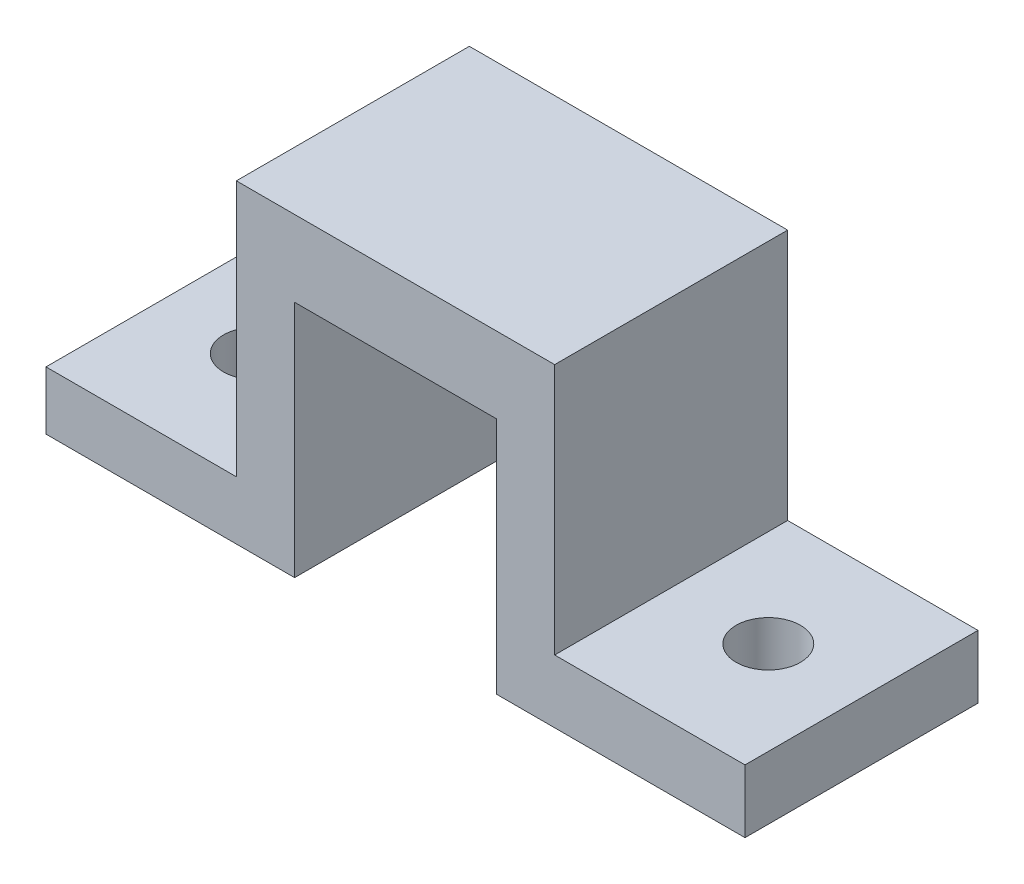
SolidWorks part; units mm, degrees
ref_plane "Front" through (0, 0, 0) normal (0, 0, 1) x (1, 0, 0)
ref_plane "Top" through (0, 0, 0) normal (0, 1, 0) x (1, 0, 0)
ref_plane "Right" through (0, 0, 0) normal (1, 0, 0) x (0, 0, -1)
sketch "Sketch1" plane through (0, 0, 0) normal (0, 0, 1) x (1, 0, 0)
  line L0 (-5.5, -6.5) -> (-19.05, -6.5)
  line L2 (-5.5, -6.5) -> (-5.5, 6.5)
  line L3 (-5.5, 6.5) -> (5.5, 6.5)
  line L4 (5.5, -6.5) -> (5.5, 6.5)
  line L5 (-5.5, -6.5) -> (5.5, 6.5) construction
  line L6 (-5.5, 6.5) -> (5.5, -6.5) construction
  line L7 (-19.05, -6.5) -> (-19.05, -3.325)
  line L8 (-19.05, -3.325) -> (-8.675, -3.325)
  line L9 (-8.675, -3.325) -> (-8.675, 10.645)
  line L10 (-8.675, 10.645) -> (8.675, 10.645)
  line L11 (8.675, 10.645) -> (8.675, -3.063)
  line L12 (8.675, -3.063) -> (19.05, -3.063)
  line L13 (19.05, -3.063) -> (19.05, -6.5)
  line L14 (19.05, -6.5) -> (5.5, -6.5)
  point P0 (0, 0)
  dimension "D1" = 11
  dimension "D2" = 13
  dimension "D3" = 3.175
  dimension "D4" = 17.145
  dimension "D5" = 3.175
  dimension "D6" = 3.175
  dimension "D7" = 19.05
  dimension "D8" = 19.05
extrude "Boss-Extrude1" add sketch "Sketch1" along normal blind 12.7
sketch "Sketch2" plane through (0, -3.325, 0) normal (0, 1, 0) x (1, 0, 0)
  line L2 (-19.05, -12.7) -> (-19.05, 0) construction
  circle A1 centre (-13.97, -6.35) radius 1.7526
  dimension "D3" = 3.5052
  dimension "D4" = 5.08
extrude "Cut-Extrude3" cut sketch "Sketch2" against normal through all
sketch "Sketch3" plane through (0, -3.063, 0) normal (0, 1, 0) x (1, 0, 0)
  line L0 (19.05, -12.7) -> (19.05, 0) construction
  circle A0 centre (13.97, -6.35) radius 1.7526
  dimension "D1" = 3.5052
  dimension "D2" = 5.08
extrude "Cut-Extrude4" cut sketch "Sketch3" against normal through all
